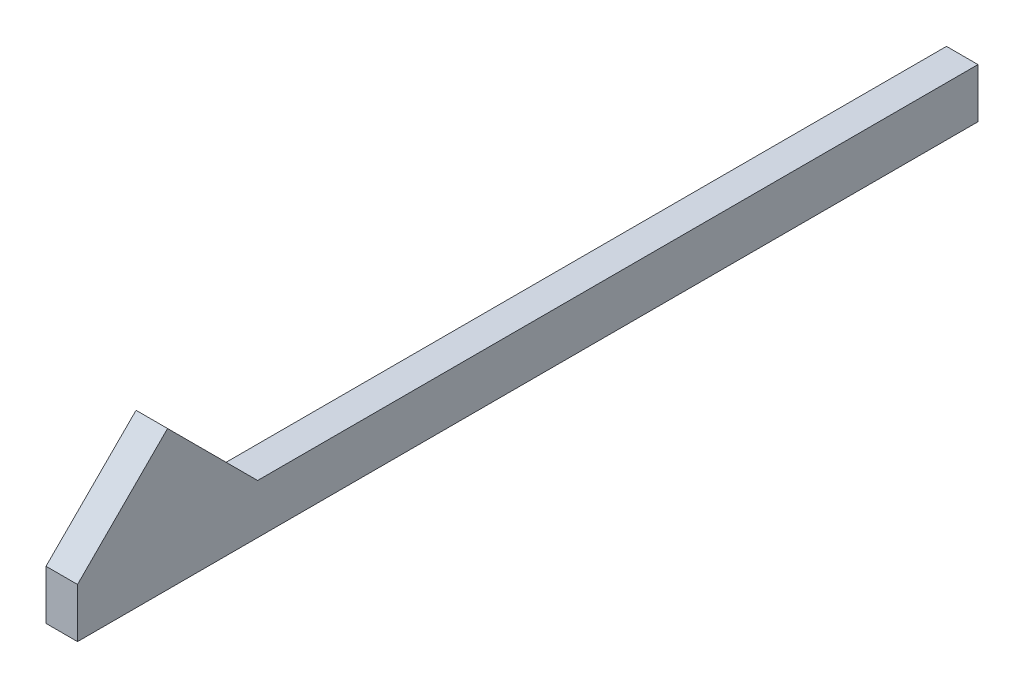
SolidWorks part; units mm, degrees
ref_plane "Plan de face" through (0, 0, 0) normal (0, 0, 1) x (1, 0, 0)
ref_plane "Plan de dessus" through (0, 0, 0) normal (0, 1, 0) x (1, 0, 0)
ref_plane "Plan de droite" through (0, 0, 0) normal (1, 0, 0) x (0, 0, -1)
sketch "Esquisse1" plane through (0, 0, 0) normal (0, 0, 1) x (1, 0, 0)
  line L1 (0, 0) -> (3.5, 0)
  line L2 (0, 0) -> (0, 5.5)
  line L3 (0, 5.5) -> (3.5, 5.5)
  line L4 (3.5, 0) -> (3.5, 5.5)
  dimension "D1" = 3.5
  dimension "D2" = 5.5
extrude "Boss.-Extru.1" add sketch "Esquisse1" against normal blind 100
sketch "Esquisse2" plane through (0, 0, 0) normal (-1, 0, 0) x (0, 0, 1)
  line L0 (0, 5.5) -> (-10, 5.5)
  line L1 (-100, 5.5) -> (0, 5.5) construction
  line L3 (-10, 15.5) -> (0, 5.5)
  line L4 (-10, 15.5) -> (-20, 5.5)
  line L5 (-20, 5.5) -> (-10, 5.5)
  dimension "D1" = 20
  dimension "D2" = 10
extrude "Boss.-Extru.2" add sketch "Esquisse2" against normal blind 3.5
